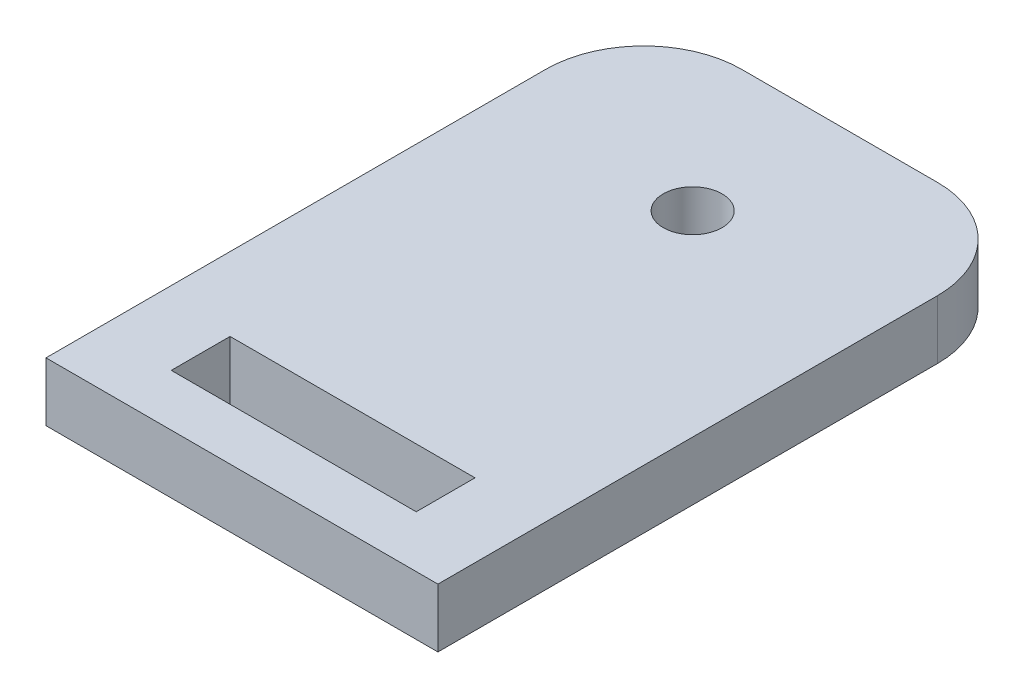
SolidWorks part; units mm, degrees
ref_plane "Front Plane" through (0, 0, 0) normal (0, 0, 1) x (1, 0, 0)
ref_plane "Top Plane" through (0, 0, 0) normal (0, 1, 0) x (1, 0, 0)
ref_plane "Right Plane" through (0, 0, 0) normal (1, 0, 0) x (0, 0, -1)
sketch "Sketch1" plane through (0, 0, 0) normal (0, 1, 0) x (1, 0, 0)
  line L0 (-18.982, -27.5) -> (21.018, -27.5)
  line L1 (-8.982, 33.5) -> (11.018, 33.5)
  line L4 (1.018, 33.5) -> (1.018, 18.5) construction
  line L8 (-18.982, 23.5) -> (-18.982, -27.5)
  line L9 (21.018, 23.5) -> (21.018, -27.5)
  line L11 (1.018, -27.5) -> (1.018, -19.2143) construction
  line L14 (-11.482, -16.2143) -> (13.518, -16.2143)
  line L15 (-11.482, -16.2143) -> (-11.482, -22.2143)
  line L16 (-11.482, -22.2143) -> (13.518, -22.2143)
  line L17 (13.518, -16.2143) -> (13.518, -22.2143)
  line L18 (-11.482, -16.2143) -> (13.518, -22.2143) construction
  line L19 (-11.482, -22.2143) -> (13.518, -16.2143) construction
  arc A0 (11.018, 33.5) -> (21.018, 23.5) centre (11.018, 23.5) cw
  arc A1 (-8.982, 33.5) -> (-18.982, 23.5) centre (-8.982, 23.5) ccw
  circle A2 centre (1.018, 18.5) radius 3
  point P0 (1.018, -26.2143)
  dimension "D2" = 6
  dimension "D3" = 10
  dimension "D1" = 15
  dimension "D4" = 61
  dimension "D5" = 40
extrude "Boss-Extrude1" add sketch "Sketch1" along normal blind 6
